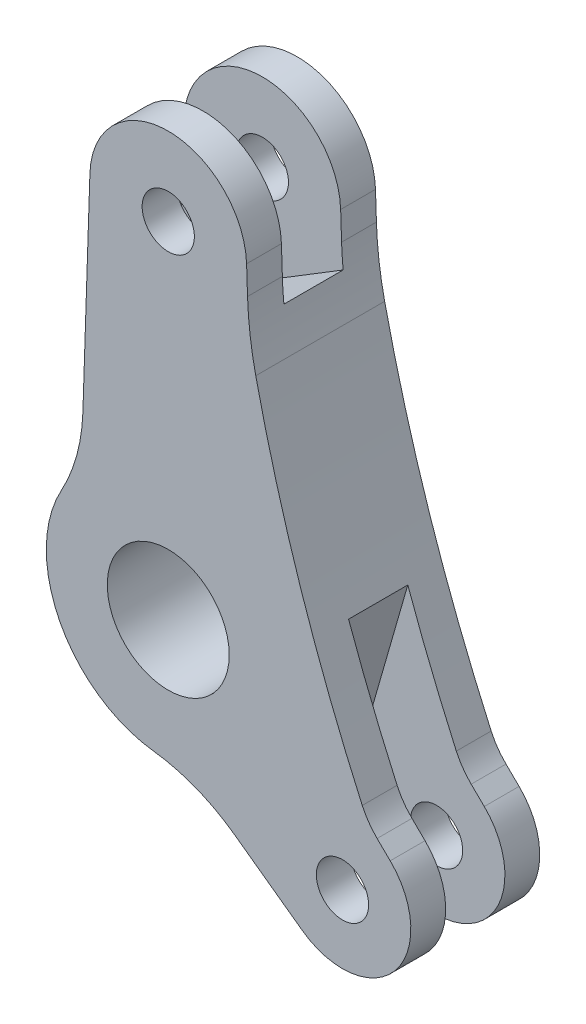
SolidWorks part; units mm, degrees
ref_plane "Front" through (0, 0, 0) normal (0, 0, 1) x (1, 0, 0)
ref_plane "Top" through (0, 0, 0) normal (0, 1, 0) x (1, 0, 0)
ref_plane "Right" through (0, 0, 0) normal (1, 0, 0) x (0, 0, -1)
sketch "Sketch1" plane through (0, 0, 0) normal (0, 0, 1) x (1, 0, 0)
  line L0 (-2.2487, 9.9751) -> (-2.4506, 3.9295)
  line L1 (1.8988, -4.3873) -> (3.8495, -5.8001)
  line L2 (2.2487, 9.9751) -> (2.2755, 9.1745)
  line L3 (5.9947, -2.4383) -> (6.3711, -2.8053)
  line L4 (0, 0) -> (6.5022, -5.4746) construction
  line L5 (0, 0) -> (0, 12.15) construction
  circle A0 centre (0, 0) radius 1.75
  circle A2 centre (0, 9.9) radius 0.75
  circle A3 centre (5.0008, -4.2105) radius 0.75
  arc A4 (-3.0667, 1.6867) -> (-0.4257, -3.474) centre (0, 0) ccw
  arc A6 (3.8495, -5.8001) -> (6.3711, -2.8053) centre (5.0008, -4.2105) ccw
  arc A8 (-2.2487, 9.9751) -> (2.2487, 9.9751) centre (0, 9.9) cw
  arc A10 (2.5116, 7.323) -> (5.5685, -1.8299) centre (48.7362, 17.6741) ccw
  arc A11 (2.5116, 7.323) -> (2.2755, 9.1745) centre (12.2699, 9.5082) cw
  arc A12 (5.5685, -1.8299) -> (5.9947, -2.4383) centre (7.3911, -1.0064) ccw
  arc A13 (-2.4506, 3.9295) -> (-3.0667, 1.6867) centre (-7.4478, 4.0964) cw
  arc A14 (-0.4257, -3.474) -> (1.8988, -4.3873) centre (-1.034, -8.4369) cw
  dimension "D1" = 3.5
  dimension "D2" = 3.5
  dimension "D3" = 9.9
  dimension "D4" = 1.5
  dimension "D6" = 2.25
  dimension "D8" = 10
  dimension "D9" = 2
  dimension "D10" = 5
  dimension "D7" = 5
  dimension "D5" = 8.5
extrude "Boss-Extrude1" add sketch "Sketch1" along normal mid plane 3.7
sketch "Sketch2" plane through (0, 0, 0) normal (0, 0, 1) x (1, 0, 0)
  line L0 (1.7049, -6.9865) -> (4.176, 1.6039)
  line L2 (1.7049, -6.9865) -> (6.1796, -9.7718)
  line L3 (6.1796, -9.7718) -> (8.2148, -2.7065)
  line L4 (8.2148, -2.7065) -> (4.176, 1.6039)
  line L5 (-2.3942, 5.6198) -> (2.3202, 8.5065)
  line L6 (2.3202, 8.5065) -> (8.5398, 16.6387)
  line L7 (8.5398, 16.6387) -> (-7.892, 11.7709)
  line L8 (-7.892, 11.7709) -> (-2.3942, 5.6198)
  line L10 (-2.2487, 9.9751) -> (-2.4506, 3.9295) construction
  arc A1 (2.2755, 9.1745) -> (2.5116, 7.323) centre (12.2699, 9.5082) ccw construction
  arc A2 (2.5116, 7.323) -> (5.5685, -1.8299) centre (48.7362, 17.6741) ccw construction
extrude "Cut-Extrude1" cut sketch "Sketch2" against normal mid plane 1.7
sketch "Sketch3" plane through (0, 0, 1.85) normal (0, 0, -1) x (-1, 0, 0)
  line L4 (2.4506, 3.9295) -> (2.2487, 9.9751)
  line L5 (-2.2487, 9.9751) -> (-2.2755, 9.1745)
  line L6 (-5.9947, -2.4383) -> (-6.3711, -2.8053)
  line L7 (-3.8495, -5.8001) -> (-1.8988, -4.3873)
  line L8 (2.4506, 3.9295) -> (2.2487, 9.9751)
  line L9 (-2.2487, 9.9751) -> (-2.2755, 9.1745)
  line L10 (-5.9947, -2.4383) -> (-6.3711, -2.8053)
  line L11 (-3.8495, -5.8001) -> (-1.8988, -4.3873)
  circle A0 centre (-5.0008, -4.2105) radius 0.75 construction
  circle A1 centre (0, 0) radius 1.75 construction
  circle A2 centre (0, 9.9) radius 0.75 construction
  circle A3 centre (-5.0008, -4.2105) radius 0.75
  circle A4 centre (0, 0) radius 1.75
  circle A5 centre (0, 9.9) radius 0.75
  arc A8 (0.4257, -3.474) -> (-1.8988, -4.3873) centre (1.034, -8.4369) ccw
  arc A9 (0.4257, -3.474) -> (3.0667, 1.6867) centre (0, 0) ccw
  arc A10 (2.4506, 3.9295) -> (3.0667, 1.6867) centre (7.4478, 4.0964) ccw
  arc A11 (2.2487, 9.9751) -> (-2.2487, 9.9751) centre (0, 9.9) ccw
  arc A12 (-2.5116, 7.323) -> (-2.2755, 9.1745) centre (-12.2699, 9.5082) ccw
  arc A13 (-5.5685, -1.8299) -> (-2.5116, 7.323) centre (-48.7362, 17.6741) ccw
  arc A14 (-5.9947, -2.4383) -> (-5.5685, -1.8299) centre (-7.3911, -1.0064) ccw
  arc A15 (-6.3711, -2.8053) -> (-3.8495, -5.8001) centre (-5.0008, -4.2105) ccw
  arc A16 (0.4257, -3.474) -> (-1.8988, -4.3873) centre (1.034, -8.4369) ccw
  arc A17 (0.4257, -3.474) -> (3.0667, 1.6867) centre (0, 0) ccw
  arc A18 (2.4506, 3.9295) -> (3.0667, 1.6867) centre (7.4478, 4.0964) ccw
  arc A19 (2.2487, 9.9751) -> (-2.2487, 9.9751) centre (0, 9.9) ccw
  arc A20 (-2.5116, 7.323) -> (-2.2755, 9.1745) centre (-12.2699, 9.5082) ccw
  arc A21 (-5.5685, -1.8299) -> (-2.5116, 7.323) centre (-48.7362, 17.6741) ccw
  arc A22 (-5.9947, -2.4383) -> (-5.5685, -1.8299) centre (-7.3911, -1.0064) ccw
  arc A23 (-6.3711, -2.8053) -> (-3.8495, -5.8001) centre (-5.0008, -4.2105) ccw
  dimension "D1" = 0
extrude "Boss-Extrude2" [suppressed] add sketch "Sketch3" against normal blind 1
